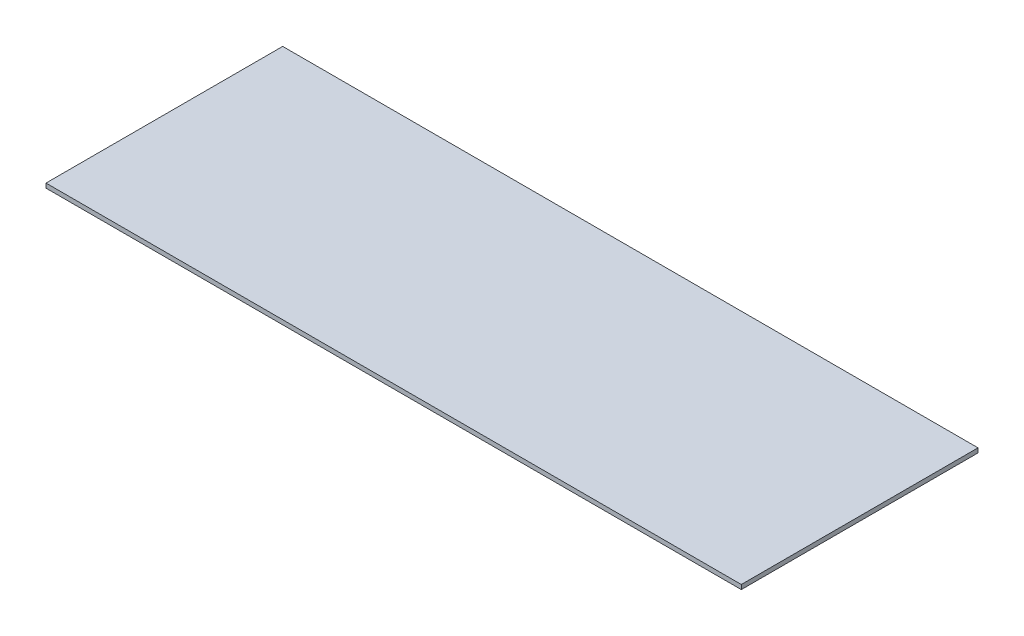
SolidWorks part; units mm, degrees
material "Pino"
ref_plane "Alzado" through (0, 0, 0) normal (0, 0, 1) x (1, 0, 0)
ref_plane "Planta" through (0, 0, 0) normal (0, 1, 0) x (1, 0, 0)
ref_plane "Vista lateral" through (0, 0, 0) normal (1, 0, 0) x (0, 0, -1)
sketch "Sketch1" plane through (0, 0, 0) normal (0, 1, 0) x (1, 0, 0)
  line L1 (-235, -80) -> (235, -80)
  line L2 (-235, -80) -> (-235, 80)
  line L3 (-235, 80) -> (235, 80)
  line L4 (235, -80) -> (235, 80)
  line L5 (-235, -80) -> (235, 80) construction
  line L6 (-235, 80) -> (235, -80) construction
  point P0 (0, 0)
  dimension "D1" = 470
  dimension "D2" = 160
extrude "Extrude1" add sketch "Sketch1" along normal blind 3
